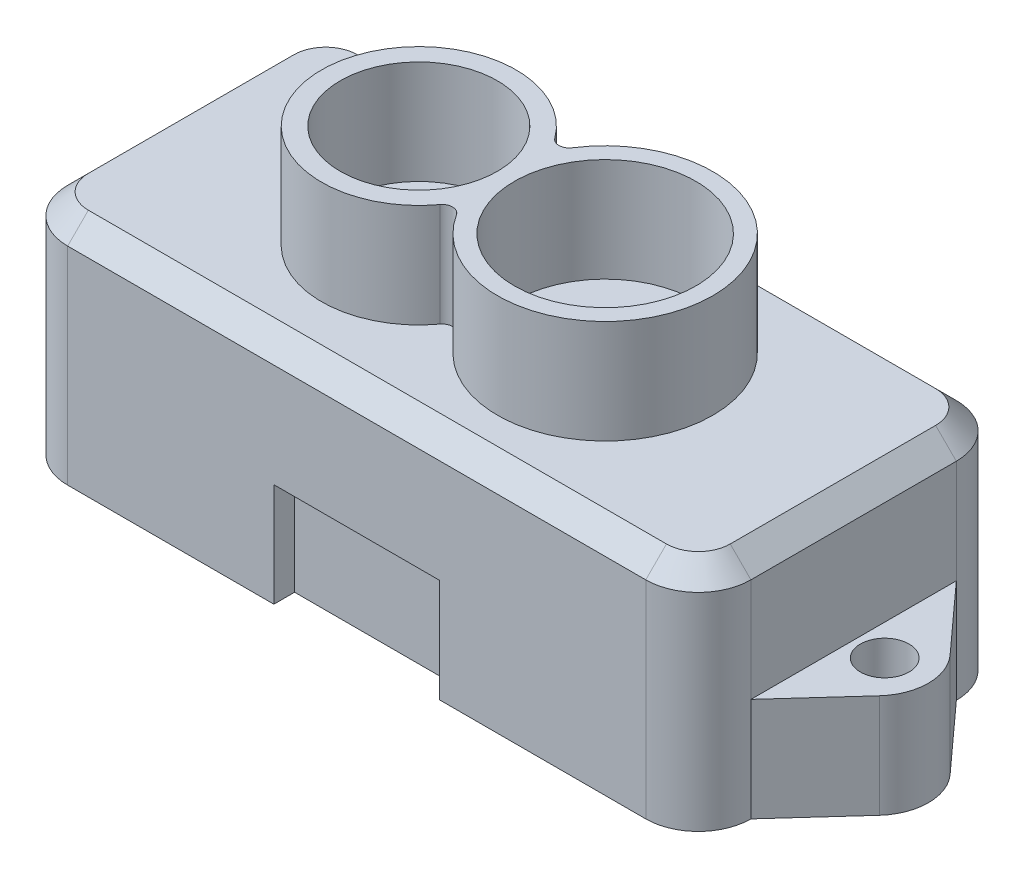
SolidWorks part; units mm, degrees
material "ABS"
ref_plane "Front Plane" through (0, 0, 0) normal (0, 0, 1) x (1, 0, 0)
ref_plane "Top Plane" through (0, 0, 0) normal (0, 1, 0) x (1, 0, 0)
ref_plane "Right Plane" through (0, 0, 0) normal (1, 0, 0) x (0, 0, -1)
sketch "Sketch1" plane through (0, 0, 0) normal (0, 1, 0) x (1, 0, 0)
  line L1 (-13.96, 7.5) -> (13.96, 7.5)
  line L2 (-16.5, 4.96) -> (-16.5, -4.96)
  line L3 (-13.96, -7.5) -> (13.96, -7.5)
  line L4 (16.5, 4.96) -> (16.5, -4.96)
  line L5 (-16.5, 7.5) -> (16.5, -7.5) construction
  line L6 (-16.5, -7.5) -> (16.5, 7.5) construction
  arc A0 (13.96, 7.5) -> (16.5, 4.96) centre (13.96, 4.96) cw
  arc A1 (13.96, -7.5) -> (16.5, -4.96) centre (13.96, -4.96) ccw
  arc A2 (-16.5, -4.96) -> (-13.96, -7.5) centre (-13.96, -4.96) ccw
  arc A3 (-13.96, 7.5) -> (-16.5, 4.96) centre (-13.96, 4.96) ccw
  point P0 (0, 0)
  dimension "D3" = 2.54
  dimension "D1" = 33
  dimension "D2" = 15
extrude "Boss-Extrude1" add sketch "Sketch1" along normal mid plane 11
sketch "Sketch2" plane through (0, -5.5, 0) normal (0, -1, 0) x (1, 0, 0)
  line L0 (-16.5, 4.96) -> (-19.4516, 1.7067)
  line L1 (-19.4516, -1.7067) -> (-16.5, -4.96)
  line L2 (-16.5, -4.96) -> (16.5, -4.96)
  line L3 (16.5, -4.96) -> (19.4516, -1.7067)
  line L4 (19.4516, 1.7067) -> (16.5, 4.96)
  line L5 (16.5, 4.96) -> (-15.9388, 4.96)
  line L6 (-15.9388, 4.96) -> (-16.5, 4.96)
  arc A0 (19.4516, -1.7067) -> (19.4516, 1.7067) centre (17.5704, 0) ccw
  arc A1 (-19.4516, 1.7067) -> (-19.4516, -1.7067) centre (-17.5704, 0) ccw
  circle A2 centre (-18, 0) radius 1.175
  circle A3 centre (18, 0) radius 1.175
  point P16 (21, 0)
  point P19 (-21, 0)
  point P22 (0, 0)
  dimension "D3" = 2.54
  dimension "D6" = 2.35
  dimension "D1" = 42
  dimension "D2" = 21
  dimension "D4" = 36
  dimension "D5" = 18
extrude "Boss-Extrude2" add sketch "Sketch2" against normal blind 5
chamfer "Chamfer1" distance 1 angle 45 8 edges at (0, 5.5, -7.5) (-15.7561, 5.5, -6.7561) (15.7561, 5.5, -6.7561) (-16.5, 5.5, 0) (16.5, 5.5, 0) (-15.7561, 5.5, 6.7561) (15.7561, 5.5, 6.7561) (0, 5.5, 7.5)
sketch "Sketch3" plane through (0, 5.5, 0) normal (0, 1, 0) x (1, 0, 0)
  arc A0 (-0.7064, 2.7746) -> (-0.7064, -2.7746) centre (-4.5, 0) ccw
  arc A1 (0.1185, -2.8005) -> (0.1185, 2.8005) centre (4.5, 0) ccw
  arc A2 (0.1185, -2.8005) -> (-0.7064, -2.7746) centre (-0.3028, -3.0697) ccw
  arc A3 (0.1185, 2.8005) -> (-0.7064, 2.7746) centre (-0.3028, 3.0697) cw
  circle A4 centre (-4.5, 0) radius 3.7936
  circle A5 centre (4.5, 0) radius 4.3815
  dimension "D3" = 9.4
  dimension "D4" = 10.4
  dimension "D5" = 0.5
  dimension "D1" = 9
  dimension "D2" = 4.5
extrude "Boss-Extrude3" add sketch "Sketch3" along normal blind 5
sketch "Sketch4" plane through (0, 0, 7.5) normal (0, 0, 1) x (1, 0, 0)
  line L0 (-13.96, -5.5) -> (13.96, -5.5) construction
  line L1 (-4, -0.5) -> (4, -0.5)
  line L2 (-4, -0.5) -> (-4, -5.5)
  line L3 (-4, -5.5) -> (4, -5.5)
  line L4 (4, -0.5) -> (4, -5.5)
  line L5 (-4, -0.5) -> (4, -5.5) construction
  line L6 (-4, -5.5) -> (4, -0.5) construction
  point P0 (0, -3)
  point P7 (0, 0)
  dimension "D1" = 8
  dimension "D2" = 5
extrude "Cut-Extrude1" cut sketch "Sketch4" against normal blind 1
equation "\"D2@Sketch2\"=\"D1@Sketch2\"/2"
equation "\"D5@Sketch2\"=\"D4@Sketch2\"/2"
equation "\"D2@Sketch3\"=\"D1@Sketch3\"/2"
